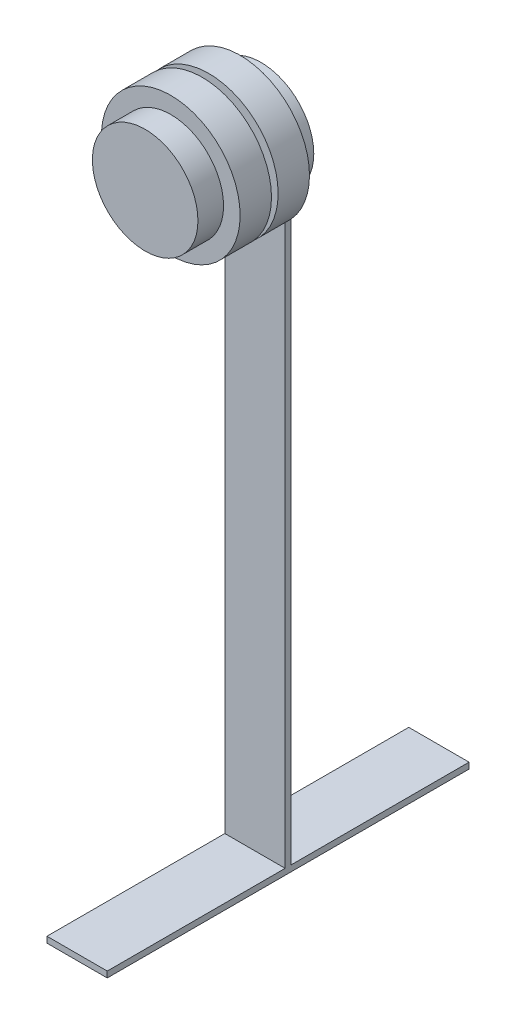
SolidWorks part; units mm, degrees
material "1023 Carbon Steel Sheet (SS)"
ref_plane "Front Plane" through (0, 0, 0) normal (0, 0, 1) x (1, 0, 0)
ref_plane "Top Plane" through (0, 0, 0) normal (0, 1, 0) x (1, 0, 0)
ref_plane "Right Plane" through (0, 0, 0) normal (1, 0, 0) x (0, 0, -1)
sketch "Sketch1" plane through (0, 0, 0) normal (0, 0, 1) x (1, 0, 0)
  circle A0 centre (0, 0) radius 22.225
  dimension "D1" = 44.45
extrude "Hub Center" add sketch "Sketch1" along normal blind 25.4 and the other way blind 23.4
sketch "Sketch2" plane through (0, 0, 0) normal (0, 0, 1) x (1, 0, 0)
  circle A0 centre (0, 0) radius 29.21
  dimension "D1" = 58.42
extrude "Inner Bearing" add sketch "Sketch2" along normal blind 13.208 from offset 1.397
sketch "Sketch3" plane through (0, 0, 0) normal (0, 0, 1) x (1, 0, 0)
  circle A0 centre (0, 0) radius 29.21
  circle A1 centre (0, 0) radius 29.21 construction
extrude "Outer Bearing" add sketch "Sketch3" against normal blind 13.208 from offset 1.397 offset against normal yes
sketch "Sketch4" plane through (0, 0, -23.4) normal (0, 0, -1) x (-1, 0, 0)
  line L0 (-12.7, -18.239) -> (-12.7, -266.7)
  line L1 (-12.7, -266.7) -> (12.7, -266.7)
  line L2 (12.7, -266.7) -> (12.7, -18.239)
  arc A0 (-12.7, -18.239) -> (12.7, -18.239) centre (0, 0) ccw
  circle A1 centre (0, 0) radius 22.225 construction
  point P6 (0, -22.225)
  dimension "D1" = 25.4
  dimension "D2" = 266.7
extrude "Tire Arm" add sketch "Sketch4" against normal blind 2.54
sketch "Sketch5" plane through (0, -266.7, 0) normal (0, -1, 0) x (1, 0, 0)
  line L0 (-12.7, -20.86) -> (12.7, -23.4) construction
  line L1 (12.7, -98.33) -> (-12.7, -98.33)
  line L2 (12.7, -98.33) -> (12.7, 54.07)
  line L3 (12.7, 54.07) -> (-12.7, 54.07)
  line L4 (-12.7, -98.33) -> (-12.7, 54.07)
  line L5 (12.7, -98.33) -> (-12.7, 54.07) construction
  line L6 (12.7, 54.07) -> (-12.7, -98.33) construction
  point P0 (0, -22.13)
  dimension "D1" = 152.4
  dimension "D2" = 25.4
extrude "Tire Contact Patch" add sketch "Sketch5" against normal blind 2.54
